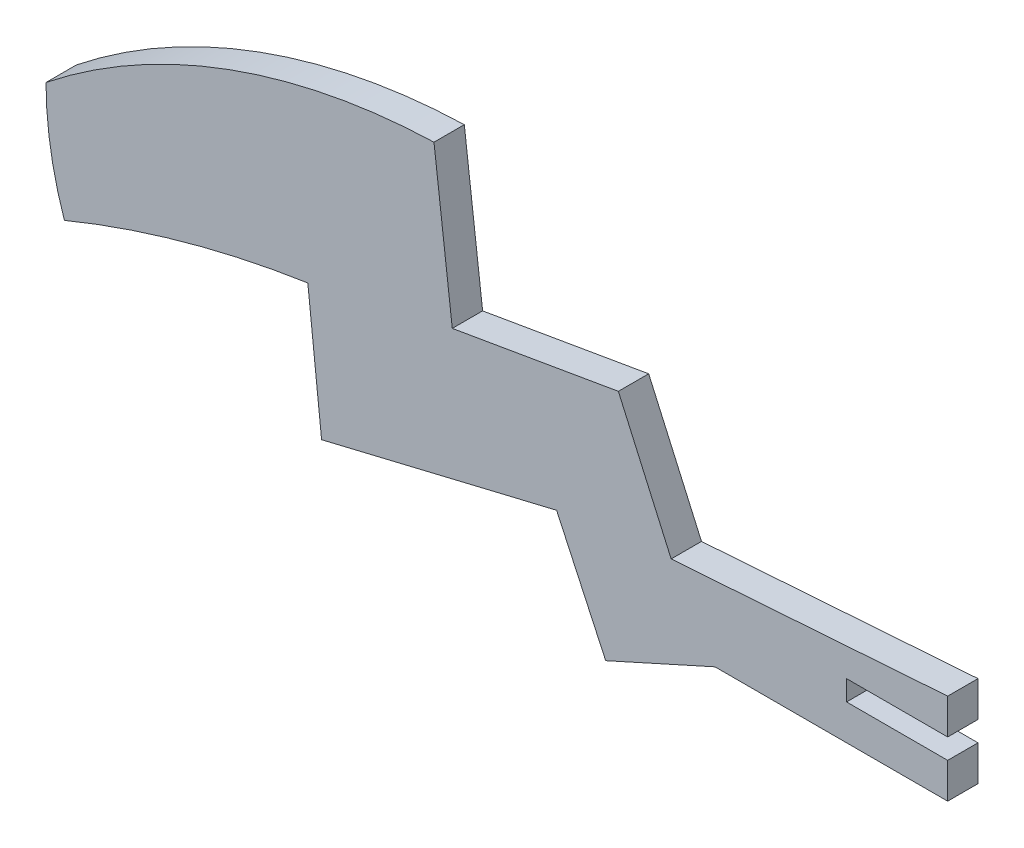
SolidWorks part; units mm, degrees
ref_plane "Alzado" through (0, 0, 0) normal (0, 0, 1) x (1, 0, 0)
ref_plane "Planta" through (0, 0, 0) normal (0, 1, 0) x (1, 0, 0)
ref_plane "Vista lateral" through (0, 0, 0) normal (1, 0, 0) x (0, 0, -1)
sketch "Model" plane through (0, 0, 0) normal (0, 0, 1) x (1, 0, 0)
  line L0 (78.5126, 8.4804) -> (67.5032, 8.4804)
  line L1 (67.5032, 8.4804) -> (55.4938, 8.4804)
  line L2 (29.5126, 24.4804) -> (27.7031, 39.5276)
  line L3 (45.9389, 27.3045) -> (29.5126, 24.4804)
  line L4 (51.1613, 15.5555) -> (45.9389, 27.3045)
  line L5 (39.8319, 14.0606) -> (16.5861, 8.4804)
  line L6 (44.6871, 3.6032) -> (39.8319, 14.0606)
  line L7 (55.4938, 8.4804) -> (44.6871, 3.6032)
  line L8 (16.5861, 8.4804) -> (15.2237, 21.2265)
  line L9 (68.5126, 11.9804) -> (78.5126, 11.9804)
  line L10 (68.5126, 13.9804) -> (68.5126, 11.9804)
  line L11 (78.5126, 13.9804) -> (68.5126, 13.9804)
  line L12 (78.5126, 17.4804) -> (78.5126, 13.9804)
  line L13 (78.5126, 17.4804) -> (51.1613, 15.5555)
  line L15 (78.5126, 11.9804) -> (78.5126, 8.4804)
  arc A0 (27.7031, 39.5276) -> (-10.6739, 25.4538) centre (29.7132, -25.3144) ccw
  arc A1 (15.2237, 21.2265) -> (-8.8542, 14.5525) centre (30.7069, -81.4039) ccw
  arc A2 (-10.6739, 25.4538) -> (-8.8542, 14.5525) centre (23.1099, 25.4907) ccw
extrude "Saliente-Extruir1" add sketch "Model" along normal blind 3
